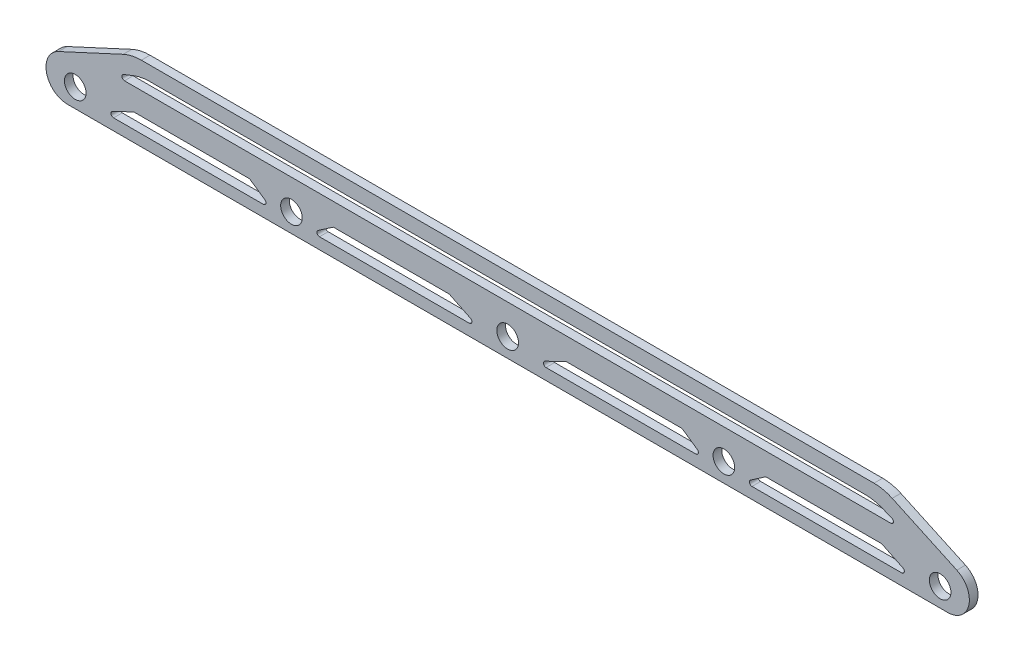
SolidWorks part; units mm, degrees
ref_plane "Front Plane" through (0, 0, 0) normal (0, 0, 1) x (1, 0, 0)
ref_plane "Top Plane" through (0, 0, 0) normal (0, 1, 0) x (1, 0, 0)
ref_plane "Right Plane" through (0, 0, 0) normal (1, 0, 0) x (0, 0, -1)
sketch "Sketch1" plane through (0, 0, 0) normal (0, 0, 1) x (1, 0, 0)
  line L1 (-84.7146, 13) -> (84.7146, 13)
  line L7 (-103.4017, 5.369) -> (-88.9154, 12.0748)
  line L11 (-82.8192, 9.6981) -> (82.8192, 9.6981)
  line L13 (-84.7146, 6.9212) -> (84.7146, 6.9212)
  line L15 (84.7146, 6.9212) -> (88.6111, 6.9212)
  line L16 (-84.7146, 6.9212) -> (-88.6111, 6.9212)
  line L17 (88.8307, 8.0796) -> (86.4785, 9.0045)
  line L18 (-88.8307, 8.0796) -> (-86.4785, 9.0045)
  line L22 (-47.5, 0) -> (-52.5, 0) construction
  line L25 (-103.4017, 5.369) -> (-103.8604, 5.1567)
  line L27 (101.76, -4.3808) -> (-101.76, -4.3808)
  line L28 (88.9154, 12.0748) -> (103.8604, 5.1567)
  line L30 (43.8549, -0.6667) -> (40.3183, 1.7613)
  line L31 (50, 6.9212) -> (50, 17.3576) construction
  line L32 (91.3924, -0.6214) -> (86.4785, 1.7613)
  line L33 (86.4785, 1.7613) -> (59.6817, 1.7613)
  line L35 (91.1306, -1.7613) -> (56.4847, -1.7613)
  line L37 (56.1451, -0.6667) -> (59.6817, 1.7613)
  line L38 (8.8694, -1.7613) -> (43.5153, -1.7613)
  line L39 (50.0001, 0) -> (49.9999, 0) construction
  line L40 (8.6076, -0.6214) -> (13.5215, 1.7613)
  line L42 (13.5215, 1.7613) -> (40.3183, 1.7613)
  line L43 (-56.1451, -0.6667) -> (-59.6817, 1.7613)
  line L44 (-91.3924, -0.6214) -> (-86.4785, 1.7613)
  line L45 (-91.1306, -1.7613) -> (-56.4847, -1.7613)
  line L46 (-86.4785, 1.7613) -> (-59.6817, 1.7613)
  line L47 (-8.6076, -0.6214) -> (-13.5215, 1.7613)
  line L48 (-13.5215, 1.7613) -> (-40.3183, 1.7613)
  line L49 (-43.8549, -0.6667) -> (-40.3183, 1.7613)
  line L50 (-8.8694, -1.7613) -> (-43.5153, -1.7613)
  arc A0 (-84.7146, 13) -> (-88.9154, 12.0748) centre (-84.7146, 3) ccw
  arc A3 (84.7146, 13) -> (88.9154, 12.0748) centre (84.7146, 3) cw
  arc A7 (82.8192, 9.6981) -> (86.4785, 9.0045) centre (82.8192, -0.3019) cw
  arc A8 (-82.8192, 9.6981) -> (-86.4785, 9.0045) centre (-82.8192, -0.3019) ccw
  circle A12 centre (-100, 0) radius 2.5
  circle A13 centre (-50, 0) radius 2.5
  circle A14 centre (0, 0) radius 2.506
  circle A15 centre (100, 0) radius 2.5
  circle A16 centre (50, 0) radius 2.5
  arc A17 (101.76, -4.3808) -> (103.8604, 5.1567) centre (101.76, 0.6192) ccw
  arc A18 (-101.76, -4.3808) -> (-103.8604, 5.1567) centre (-101.76, 0.6192) cw
  arc A20 (91.1306, -1.7613) -> (91.3924, -0.6214) centre (91.1306, -1.1613) ccw
  arc A21 (88.6111, 6.9212) -> (88.8307, 8.0796) centre (88.6111, 7.5212) ccw
  arc A22 (-88.6111, 6.9212) -> (-88.8307, 8.0796) centre (-88.6111, 7.5212) cw
  arc A23 (43.8549, -0.6667) -> (43.5153, -1.7613) centre (43.5153, -1.1613) cw
  arc A24 (56.1451, -0.6667) -> (56.4847, -1.7613) centre (56.4847, -1.1613) ccw
  arc A25 (8.8694, -1.7613) -> (8.6076, -0.6214) centre (8.8694, -1.1613) cw
  arc A26 (-56.1451, -0.6667) -> (-56.4847, -1.7613) centre (-56.4847, -1.1613) cw
  arc A27 (-91.1306, -1.7613) -> (-91.3924, -0.6214) centre (-91.1306, -1.1613) cw
  arc A28 (-8.8694, -1.7613) -> (-8.6076, -0.6214) centre (-8.8694, -1.1613) ccw
  arc A29 (-43.8549, -0.6667) -> (-43.5153, -1.7613) centre (-43.5153, -1.1613) ccw
  point P0 (0, 0)
  point P4 (0, 8.3097)
  point P17 (0, -6.3904)
  dimension "D1" = 10
  dimension "D2" = 5
  dimension "D3" = 0.6
  dimension "D4" = 10
  dimension "D5" = 0.6
  dimension "D6" = 0.6
  dimension "D7" = 0.6
extrude "Boss-Extrude1" add sketch "Sketch1" along normal blind 2
